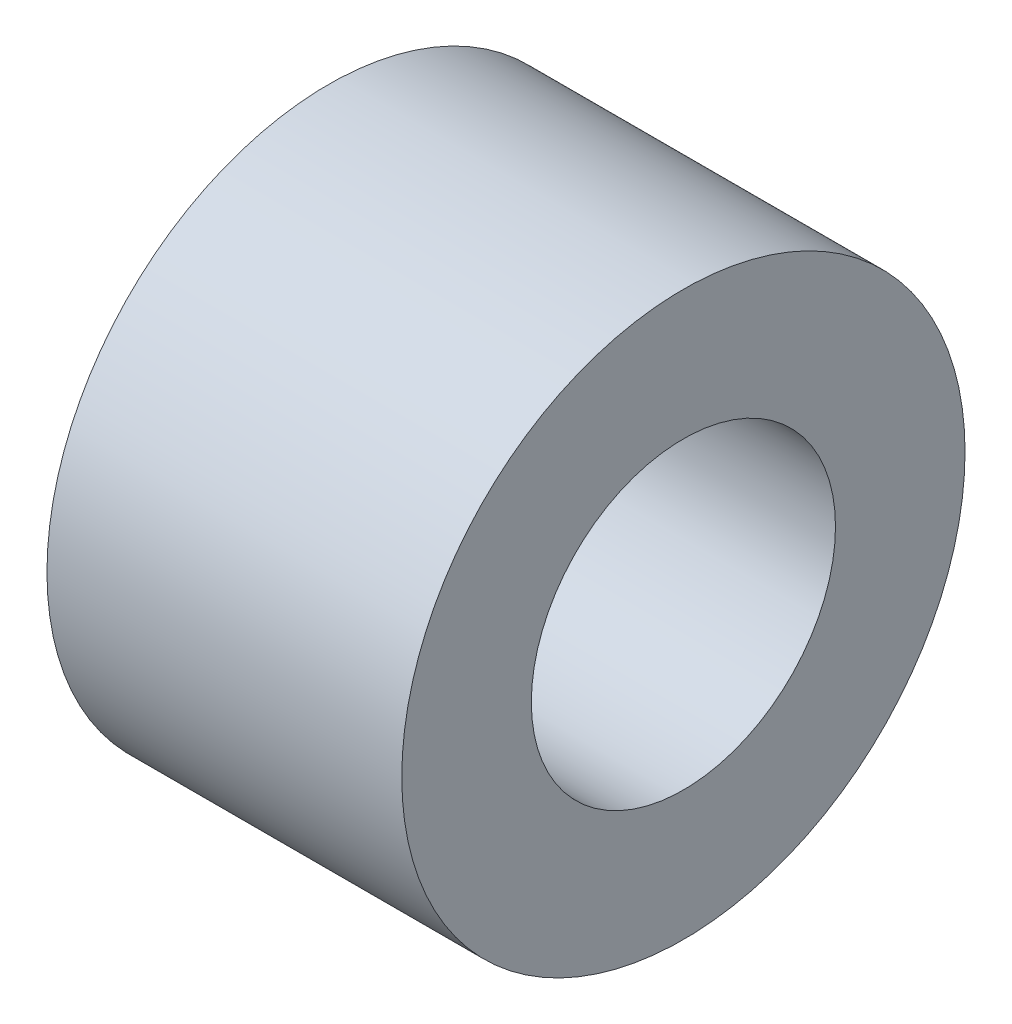
SolidWorks part; units mm, degrees
ref_plane "Plan de face" through (0, 0, 0) normal (0, 0, 1) x (1, 0, 0)
ref_plane "Plan de dessus" through (0, 0, 0) normal (0, 1, 0) x (1, 0, 0)
ref_plane "Plan de droite" through (0, 0, 0) normal (1, 0, 0) x (0, 0, -1)
sketch "Esquisse1" plane through (0, 0, 0) normal (1, 0, 0) x (0, 0, -1)
  circle A0 centre (0, 0) radius 3.429
  circle A1 centre (0, 0) radius 6.35
  dimension "D1" = 6.858
  dimension "D2" = 12.7
extrude "Boss.-Extru.1" add sketch "Esquisse1" against normal blind 8
equation "\"D1@Boss.-Extru.1\"=8mm"
